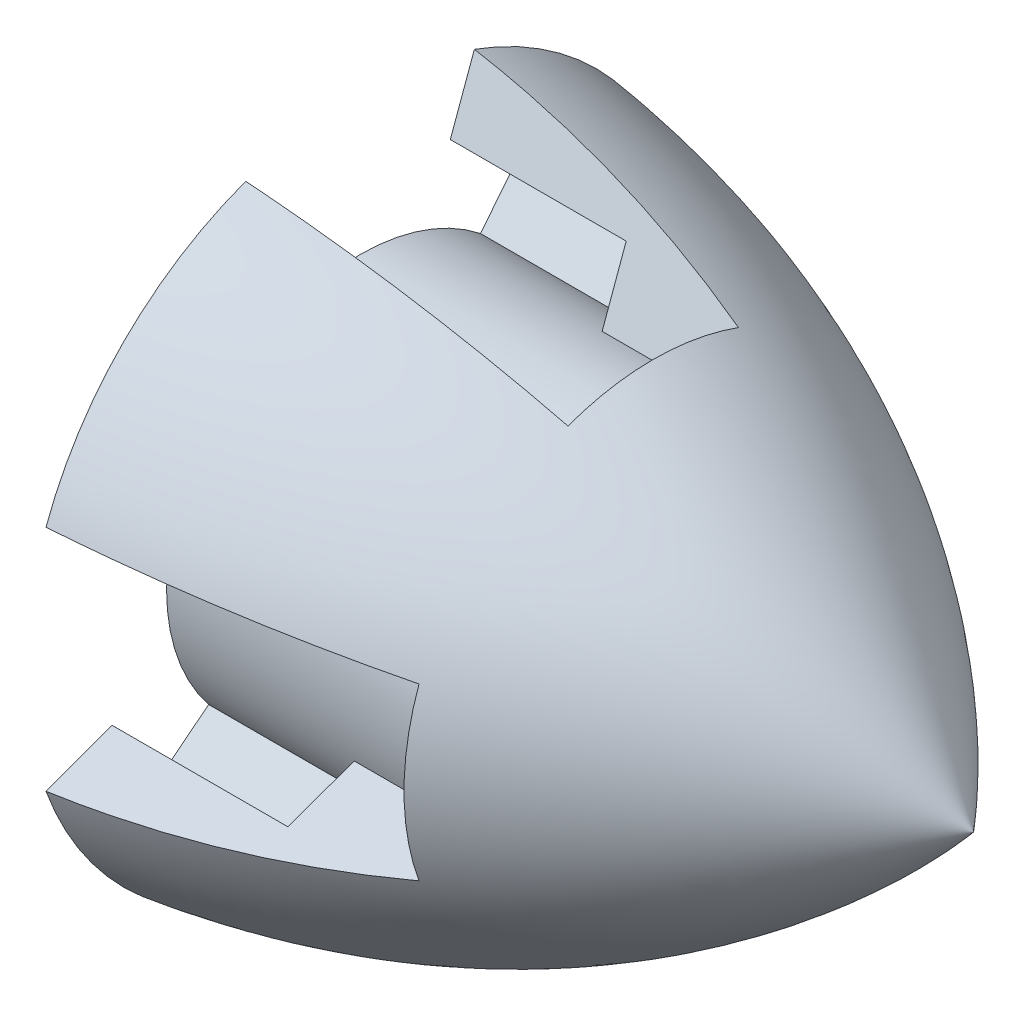
SolidWorks part; units mm, degrees
ref_plane "Спереди" through (0, 0, 0) normal (0, 0, 1) x (1, 0, 0)
ref_plane "Сверху" through (0, 0, 0) normal (0, 1, 0) x (1, 0, 0)
ref_plane "Справа" through (0, 0, 0) normal (1, 0, 0) x (0, 0, -1)
sketch "Эскиз2" plane through (0, 0, 0) normal (0, 0, 1) x (1, 0, 0)
  line L0 (0, 0) -> (0, 28.5)
  line L1 (0, 0) -> (28.5, 0)
  line L2 (-1000, 0) -> (49000, 0) construction
  line L3 (28.5, 0) -> (52.3107, 0)
  spline S0 degree 2 poles (0, 28.5) (31.309, 24.448) (52.3107, 0) knots 0 0 0 1 1 1
revolve "Повернуть1" add sketch "Эскиз2" angle 360 about L2
sketch "Эскиз7" plane through (0, 0, 0) normal (-1, 0, 0) x (0, 0, 1)
  circle A0 centre (0, 0) radius 12.6
extrude "Вырез-Вытянуть1" cut sketch "Эскиз7" against normal blind 15
sketch "Эскиз8" plane through (0, 0, 0) normal (-1, 0, 0) x (0, 0, 1)
  circle A0 centre (0, 0) radius 16.5
extrude "Вырез-Вытянуть2" cut sketch "Эскиз8" against normal blind 1
sketch "Эскиз11" plane through (0, 0, 0) normal (-1, 0, 0) x (0, 0, 1)
  line L0 (0, 0) -> (17101.0072, 46984.631) construction
  line L1 (0, 0) -> (-17101.0072, 46984.631) construction
  line L2 (-9.7476, 26.7812) -> (-7.6955, 21.1431)
  line L3 (9.7476, 26.7812) -> (7.6955, 21.1431)
  line L4 (0, 0) -> (-26124.9282, 42632.0082) construction
  line L5 (0, 0) -> (26124.9282, 42632.0082) construction
  line L8 (-7.6955, 21.1431) -> (-5.6433, 15.5049)
  line L9 (5.6433, 15.5049) -> (7.6955, 21.1431)
  arc A0 (-5.6433, 15.5049) -> (5.6433, 15.5049) centre (0, 0) cw
  circle A1 centre (0, 0) radius 16.5 construction
  arc A2 (-9.7476, 26.7812) -> (9.7476, 26.7812) centre (0, 0) cw
  circle A3 centre (0, 0) radius 28.5 construction
  circle A5 centre (0, 0) radius 22.5 construction
extrude "Вырез-Вытянуть3" cut sketch "Эскиз11" against normal blind 25
pattern_circular "Круговой массив1" count 4 over 360 about axis through (1, 0, 0) along (-1, 0, 0) of "Вырез-Вытянуть3"
sketch "Эскиз12" plane through (1, 0, 0) normal (-1, 0, 0) x (0, 0, 1)
  circle A0 centre (0, 0) radius 12.6
  circle A1 centre (0, 0) radius 16.5
extrude "Бобышка-Вытянуть1" add sketch "Эскиз12" along normal blind 1
sketch "Эскиз13" plane through (0, 0, 0) normal (-1, 0, 0) x (0, 0, 1)
  line L0 (0, 0) -> (-31125.7318, 39130.4078) construction
  line L1 (0, 0) -> (31125.7318, 39130.4078) construction
  line L2 (-14.0066, 17.6087) -> (-10.2715, 12.913)
  line L3 (10.2715, 12.913) -> (14.0066, 17.6087)
  circle A1 centre (0, 0) radius 16.5 construction
  circle A2 centre (0, 0) radius 22.5 construction
  arc A3 (-14.0066, 17.6087) -> (14.0066, 17.6087) centre (0, 0) cw
  arc A4 (10.2715, 12.913) -> (-10.2715, 12.913) centre (0, 0) ccw
extrude "Вырез-Вытянуть4" cut sketch "Эскиз13" against normal blind 15
pattern_circular "Круговой массив2" count 4 every 90 of "Вырез-Вытянуть4"
